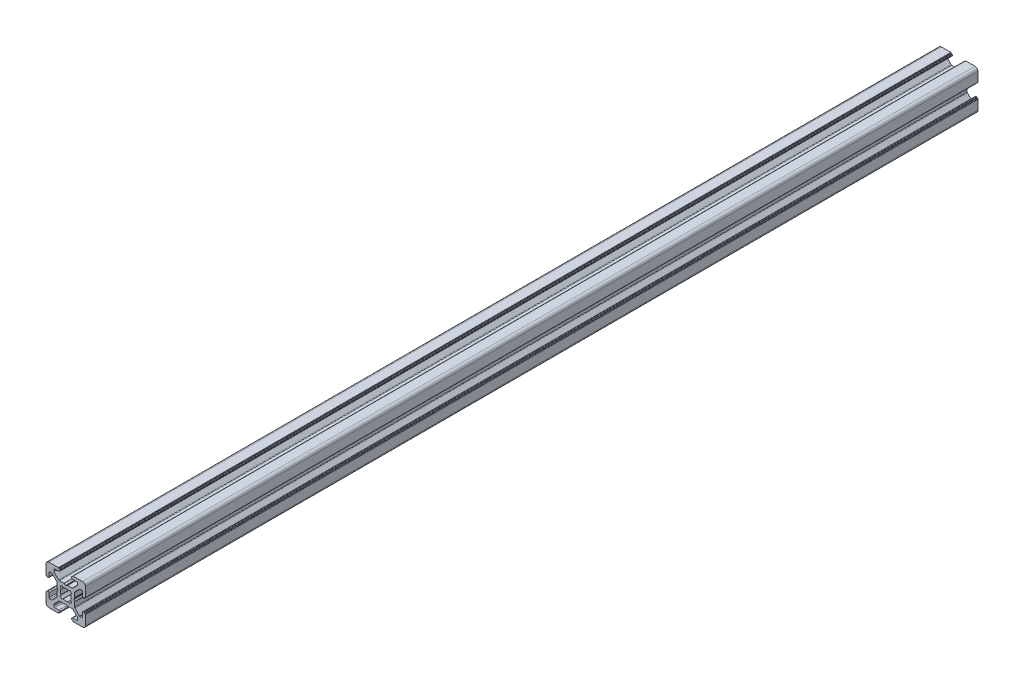
SolidWorks part; units mm, degrees
ref_plane "Front Plane" through (0, 0, 0) normal (0, 0, 1) x (1, 0, 0)
ref_plane "Top Plane" through (0, 0, 0) normal (0, 1, 0) x (1, 0, 0)
ref_plane "Right Plane" through (0, 0, 0) normal (1, 0, 0) x (0, 0, -1)
sketch "Sketch1" plane through (0, 0, 0) normal (0, 0, 1) x (1, 0, 0)
  line L0 (0, 13.3675) -> (0, -10.9159) construction
  line L1 (-12.9725, 0) -> (15.1887, 0) construction
  line L2 (-3.5, 8.5) -> (-5.5, 8.5)
  line L3 (-3.55, 9.7) -> (-3.55, 9.8)
  line L4 (-6, 7.2678) -> (-6, 8)
  line L5 (-7.2678, 6) -> (-8, 6)
  line L6 (-3.75, 10) -> (-8.5, 10)
  line L7 (-9.7, 3.55) -> (-9.8, 3.55)
  line L8 (-9.5, 3.2) -> (-9.5, 3.35)
  line L9 (-9, 3) -> (-9.3, 3)
  line L10 (-4.4732, 0.8536) -> (-4.0381, 0.1)
  line L11 (-4.5, 3.2322) -> (-4.5, 0.9536)
  line L12 (-8.5, 3.5) -> (-8.5, 5.5)
  line L13 (-10, 3.75) -> (-10, 8.5)
  line L14 (-3.5858, 4.6464) -> (-5.8536, 6.9142)
  line L15 (-4.6464, 3.5858) -> (-6.9142, 5.8536)
  line L16 (-3.2, 9.5) -> (-3.35, 9.5)
  line L17 (-3, 9) -> (-3, 9.3)
  line L18 (-0.8536, 4.4732) -> (-0.1, 4.0381)
  line L19 (-3.2322, 4.5) -> (-0.9536, 4.5)
  line L20 (-1.2582, 2.4453) -> (-1.9139, 2.9896)
  line L21 (-2.4453, 1.2582) -> (-2.9922, 1.9099)
  line L22 (3.5, -8.5) -> (5.5, -8.5)
  line L23 (3.55, -9.7) -> (3.55, -9.8)
  line L24 (6, -7.2678) -> (6, -8)
  line L25 (7.2678, -6) -> (8, -6)
  line L26 (3.75, -10) -> (8.5, -10)
  line L27 (9.7, -3.55) -> (9.8, -3.55)
  line L28 (9.5, -3.2) -> (9.5, -3.35)
  line L29 (9, -3) -> (9.3, -3)
  line L30 (4.4732, -0.8536) -> (4.0381, -0.1)
  line L31 (4.5, -3.2322) -> (4.5, -0.9536)
  line L32 (8.5, -3.5) -> (8.5, -5.5)
  line L33 (10, -3.75) -> (10, -8.5)
  line L34 (3.5858, -4.6464) -> (5.8536, -6.9142)
  line L35 (4.6464, -3.5858) -> (6.9142, -5.8536)
  line L36 (3.2, -9.5) -> (3.35, -9.5)
  line L37 (3, -9) -> (3, -9.3)
  line L38 (0.8536, -4.4732) -> (0.1, -4.0381)
  line L39 (3.2322, -4.5) -> (0.9536, -4.5)
  line L40 (1.2582, -2.4453) -> (1.9139, -2.9896)
  line L41 (2.4453, -1.2582) -> (2.9922, -1.9099)
  line L42 (-2.4453, -1.2582) -> (-2.9922, -1.9099)
  line L43 (-1.2582, -2.4453) -> (-1.9139, -2.9896)
  line L44 (-3.2322, -4.5) -> (-0.9536, -4.5)
  line L45 (-0.8536, -4.4732) -> (-0.1, -4.0381)
  line L46 (-3, -9) -> (-3, -9.3)
  line L47 (-3.2, -9.5) -> (-3.35, -9.5)
  line L48 (-4.6464, -3.5858) -> (-6.9142, -5.8536)
  line L49 (-3.5858, -4.6464) -> (-5.8536, -6.9142)
  line L50 (-10, -3.75) -> (-10, -8.5)
  line L51 (-8.5, -3.5) -> (-8.5, -5.5)
  line L52 (-4.5, -3.2322) -> (-4.5, -0.9536)
  line L53 (-4.4732, -0.8536) -> (-4.0381, -0.1)
  line L54 (-9, -3) -> (-9.3, -3)
  line L55 (-9.5, -3.2) -> (-9.5, -3.35)
  line L56 (-9.7, -3.55) -> (-9.8, -3.55)
  line L57 (2.4453, 1.2582) -> (2.9922, 1.9099)
  line L58 (1.2582, 2.4453) -> (1.9139, 2.9896)
  line L59 (3.2322, 4.5) -> (0.9536, 4.5)
  line L60 (0.8536, 4.4732) -> (0.1, 4.0381)
  line L61 (-3.75, -10) -> (-8.5, -10)
  line L62 (-7.2678, -6) -> (-8, -6)
  line L63 (-6, -7.2678) -> (-6, -8)
  line L64 (3, 9) -> (3, 9.3)
  line L65 (3.2, 9.5) -> (3.35, 9.5)
  line L66 (4.6464, 3.5858) -> (6.9142, 5.8536)
  line L67 (3.5858, 4.6464) -> (5.8536, 6.9142)
  line L68 (10, 3.75) -> (10, 8.5)
  line L69 (8.5, 3.5) -> (8.5, 5.5)
  line L70 (4.5, 3.2322) -> (4.5, 0.9536)
  line L71 (4.4732, 0.8536) -> (4.0381, 0.1)
  line L72 (9, 3) -> (9.3, 3)
  line L73 (9.5, 3.2) -> (9.5, 3.35)
  line L74 (9.7, 3.55) -> (9.8, 3.55)
  line L75 (3.75, 10) -> (8.5, 10)
  line L76 (7.2678, 6) -> (8, 6)
  line L77 (6, 7.2678) -> (6, 8)
  line L78 (3.55, 9.7) -> (3.55, 9.8)
  line L79 (3.5, 8.5) -> (5.5, 8.5)
  line L80 (-3.55, -9.7) -> (-3.55, -9.8)
  line L81 (-3.5, -8.5) -> (-5.5, -8.5)
  arc A0 (-10, 8.5) -> (-8.5, 10) centre (-8.5, 8.5) cw
  arc A1 (-8.5, 5.5) -> (-8, 6) centre (-8, 5.5) cw
  arc A2 (-7.2678, 6) -> (-6.9142, 5.8536) centre (-7.2678, 5.5) cw
  arc A3 (-5.8536, 6.9142) -> (-6, 7.2678) centre (-5.5, 7.2678) cw
  arc A4 (-6, 8) -> (-5.5, 8.5) centre (-5.5, 8) cw
  arc A5 (-9.7, 3.55) -> (-9.5, 3.35) centre (-9.7, 3.35) cw
  arc A6 (-9.8, 3.55) -> (-10, 3.75) centre (-9.8, 3.75) cw
  arc A7 (-9.3, 3) -> (-9.5, 3.2) centre (-9.3, 3.2) cw
  arc A8 (-8.5, 3.5) -> (-9, 3) centre (-9, 3.5) cw
  arc A9 (-4.6464, 3.5858) -> (-4.5, 3.2322) centre (-5, 3.2322) cw
  arc A10 (-4.4732, 0.8536) -> (-4.5, 0.9536) centre (-4.3, 0.9536) cw
  arc A11 (-4.0381, 0.1) -> (-4.0381, -0.1) centre (-4.2113, 0) cw
  arc A12 (-3.2, 9.5) -> (-3, 9.3) centre (-3.2, 9.3) cw
  arc A13 (-0.9536, 4.5) -> (-0.8536, 4.4732) centre (-0.9536, 4.3) cw
  arc A14 (-2.9922, 1.9099) -> (-1.9139, 2.9896) centre (0, 0) cw
  arc A15 (-3.2322, 4.5) -> (-3.5858, 4.6464) centre (-3.2322, 5) cw
  arc A16 (-3.75, 10) -> (-3.55, 9.8) centre (-3.75, 9.8) cw
  arc A17 (-3.35, 9.5) -> (-3.55, 9.7) centre (-3.35, 9.7) cw
  arc A18 (2.4453, -1.2582) -> (2.4453, 1.2582) centre (0, 0) ccw
  arc A19 (-3, 9) -> (-3.5, 8.5) centre (-3.5, 9) cw
  arc A20 (-2.4453, -1.2582) -> (-2.4453, 1.2582) centre (0, 0) cw
  arc A21 (10, -8.5) -> (8.5, -10) centre (8.5, -8.5) cw
  arc A22 (8.5, -5.5) -> (8, -6) centre (8, -5.5) cw
  arc A23 (7.2678, -6) -> (6.9142, -5.8536) centre (7.2678, -5.5) cw
  arc A24 (5.8536, -6.9142) -> (6, -7.2678) centre (5.5, -7.2678) cw
  arc A25 (6, -8) -> (5.5, -8.5) centre (5.5, -8) cw
  arc A26 (9.7, -3.55) -> (9.5, -3.35) centre (9.7, -3.35) cw
  arc A27 (9.8, -3.55) -> (10, -3.75) centre (9.8, -3.75) cw
  arc A28 (9.3, -3) -> (9.5, -3.2) centre (9.3, -3.2) cw
  arc A29 (8.5, -3.5) -> (9, -3) centre (9, -3.5) cw
  arc A30 (4.6464, -3.5858) -> (4.5, -3.2322) centre (5, -3.2322) cw
  arc A31 (4.4732, -0.8536) -> (4.5, -0.9536) centre (4.3, -0.9536) cw
  arc A32 (3.2, -9.5) -> (3, -9.3) centre (3.2, -9.3) cw
  arc A33 (-0.1, -4.0381) -> (0.1, -4.0381) centre (0, -4.2113) cw
  arc A34 (0.9536, -4.5) -> (0.8536, -4.4732) centre (0.9536, -4.3) cw
  arc A35 (2.9922, -1.9099) -> (1.9139, -2.9896) centre (0, 0) cw
  arc A36 (1.2582, -2.4453) -> (-1.2582, -2.4453) centre (0, 0) cw
  arc A37 (3.2322, -4.5) -> (3.5858, -4.6464) centre (3.2322, -5) cw
  arc A38 (3.75, -10) -> (3.55, -9.8) centre (3.75, -9.8) cw
  arc A39 (3.35, -9.5) -> (3.55, -9.7) centre (3.35, -9.7) cw
  arc A40 (3, -9) -> (3.5, -8.5) centre (3.5, -9) cw
  arc A41 (-3, -9) -> (-3.5, -8.5) centre (-3.5, -9) ccw
  arc A42 (-3.35, -9.5) -> (-3.55, -9.7) centre (-3.35, -9.7) ccw
  arc A43 (-3.75, -10) -> (-3.55, -9.8) centre (-3.75, -9.8) ccw
  arc A44 (-3.2322, -4.5) -> (-3.5858, -4.6464) centre (-3.2322, -5) ccw
  arc A45 (-2.9922, -1.9099) -> (-1.9139, -2.9896) centre (0, 0) ccw
  arc A46 (-0.9536, -4.5) -> (-0.8536, -4.4732) centre (-0.9536, -4.3) ccw
  arc A47 (-3.2, -9.5) -> (-3, -9.3) centre (-3.2, -9.3) ccw
  arc A48 (-4.4732, -0.8536) -> (-4.5, -0.9536) centre (-4.3, -0.9536) ccw
  arc A49 (3, 9) -> (3.5, 8.5) centre (3.5, 9) ccw
  arc A50 (3.35, 9.5) -> (3.55, 9.7) centre (3.35, 9.7) ccw
  arc A51 (3.75, 10) -> (3.55, 9.8) centre (3.75, 9.8) ccw
  arc A52 (3.2322, 4.5) -> (3.5858, 4.6464) centre (3.2322, 5) ccw
  arc A53 (1.2582, 2.4453) -> (-1.2582, 2.4453) centre (0, 0) ccw
  arc A54 (-4.6464, -3.5858) -> (-4.5, -3.2322) centre (-5, -3.2322) ccw
  arc A55 (-8.5, -3.5) -> (-9, -3) centre (-9, -3.5) ccw
  arc A56 (-9.3, -3) -> (-9.5, -3.2) centre (-9.3, -3.2) ccw
  arc A57 (-9.8, -3.55) -> (-10, -3.75) centre (-9.8, -3.75) ccw
  arc A58 (-9.7, -3.55) -> (-9.5, -3.35) centre (-9.7, -3.35) ccw
  arc A59 (-6, -8) -> (-5.5, -8.5) centre (-5.5, -8) ccw
  arc A60 (2.9922, 1.9099) -> (1.9139, 2.9896) centre (0, 0) ccw
  arc A61 (0.9536, 4.5) -> (0.8536, 4.4732) centre (0.9536, 4.3) ccw
  arc A62 (-0.1, 4.0381) -> (0.1, 4.0381) centre (0, 4.2113) ccw
  arc A63 (-5.8536, -6.9142) -> (-6, -7.2678) centre (-5.5, -7.2678) ccw
  arc A64 (-7.2678, -6) -> (-6.9142, -5.8536) centre (-7.2678, -5.5) ccw
  arc A65 (-8.5, -5.5) -> (-8, -6) centre (-8, -5.5) ccw
  arc A66 (-10, -8.5) -> (-8.5, -10) centre (-8.5, -8.5) ccw
  arc A67 (3.2, 9.5) -> (3, 9.3) centre (3.2, 9.3) ccw
  arc A68 (4.0381, 0.1) -> (4.0381, -0.1) centre (4.2113, 0) ccw
  arc A69 (4.4732, 0.8536) -> (4.5, 0.9536) centre (4.3, 0.9536) ccw
  arc A70 (4.6464, 3.5858) -> (4.5, 3.2322) centre (5, 3.2322) ccw
  arc A71 (8.5, 3.5) -> (9, 3) centre (9, 3.5) ccw
  arc A72 (9.3, 3) -> (9.5, 3.2) centre (9.3, 3.2) ccw
  arc A73 (9.8, 3.55) -> (10, 3.75) centre (9.8, 3.75) ccw
  arc A74 (9.7, 3.55) -> (9.5, 3.35) centre (9.7, 3.35) ccw
  arc A75 (6, 8) -> (5.5, 8.5) centre (5.5, 8) ccw
  arc A76 (5.8536, 6.9142) -> (6, 7.2678) centre (5.5, 7.2678) ccw
  arc A77 (7.2678, 6) -> (6.9142, 5.8536) centre (7.2678, 5.5) ccw
  arc A78 (8.5, 5.5) -> (8, 6) centre (8, 5.5) ccw
  arc A79 (10, 8.5) -> (8.5, 10) centre (8.5, 8.5) ccw
  dimension "D4" = 5.5
  dimension "D1" = 6
  dimension "D2" = 20
  dimension "D3" = 20
  dimension "D5" = 5.5
  dimension "D6" = 10
  dimension "D7" = 6
  dimension "D8" = 6
  dimension "D9" = 6
extrude "Extrude1" add sketch "Sketch1" along normal blind 452
